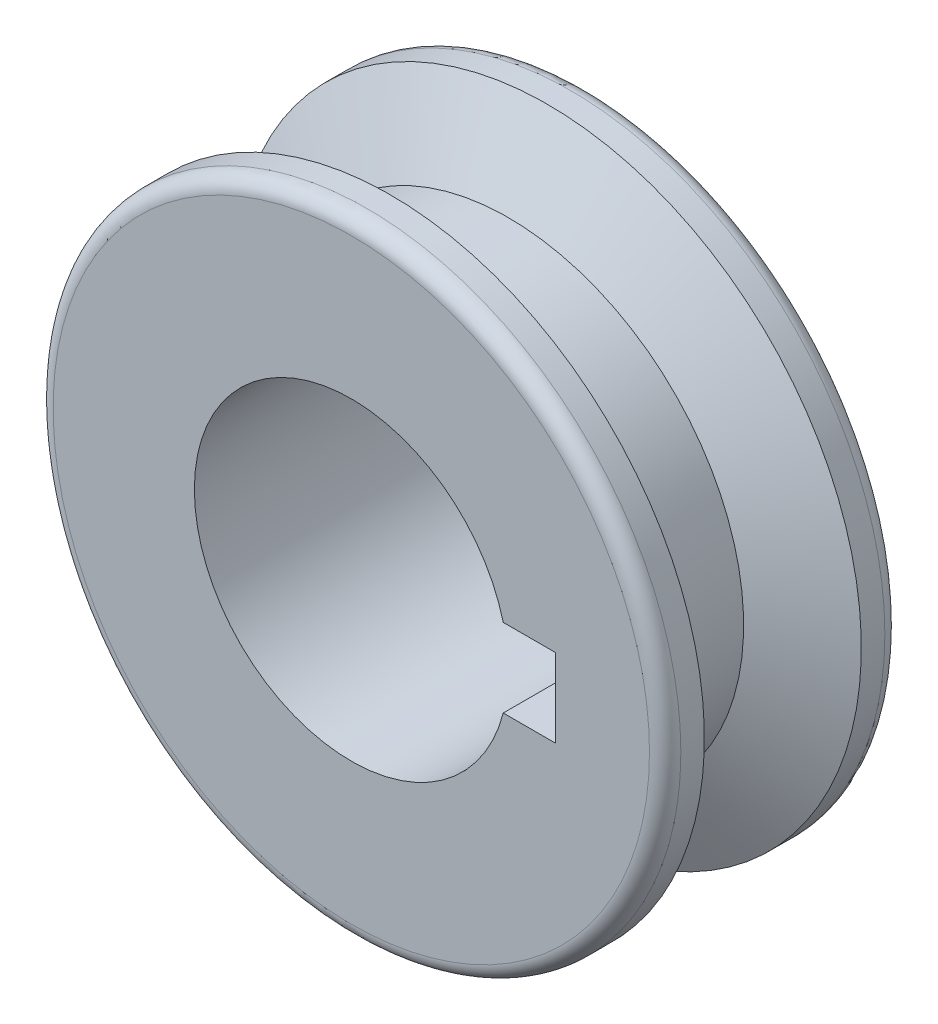
SolidWorks part; units mm, degrees
ref_plane "前视基准面" through (0, 0, 0) normal (0, 0, 1) x (1, 0, 0)
ref_plane "上视基准面" through (0, 0, 0) normal (0, 1, 0) x (1, 0, 0)
ref_plane "右视基准面" through (0, 0, 0) normal (1, 0, 0) x (0, 0, -1)
sketch "草图1" plane through (0, 0, 0) normal (0, 0, 1) x (1, 0, 0)
  circle A0 centre (0, 0) radius 10
  circle A1 centre (0, 0) radius 20
  dimension "D1" = 20
  dimension "D2" = 40
extrude "凸台-拉伸1" add sketch "草图1" along normal blind 15
sketch "草图2" plane through (0, 0, 0) normal (1, 0, 0) x (0, 0, -1)
  line L0 (0, 20) -> (-15, 20)
  line L1 (-15, 20) -> (-15, 15)
  line L2 (-15, 20) -> (-15, -20) construction
  line L3 (-15, 15) -> (0, 15)
  line L4 (0, -20) -> (0, 20) construction
  line L6 (-2.5, 20) -> (-5, 15)
  line L8 (-12.5, 20) -> (-10, 15)
  dimension "D1" = 5
  dimension "D2" = 2.5
ref_axis "基准轴1" through (0, 0, -0.75) along (0, 0, 1)
revolve "切除-旋转1" cut sketch "草图2" angle 360 about axis through (0, 0, -0.75) along (0, 0, 1)
ref_plane "基准面1" through (10, 0, 0) normal (1, 0, 0) x (0, 0, -1)
sketch "草图3" plane through (10, 0, 0) normal (1, 0, 0) x (0, 0, -1)
  line L0 (-15.7356, 0) -> (0, 0) construction
  line L1 (-15.7356, 2.5) -> (0, 2.5)
  line L2 (-15.7356, -2.5) -> (0, -2.5)
  arc A0 (-15.7356, 2.5) -> (-15.7356, -2.5) centre (-15.7356, 0) ccw
  arc A1 (0, -2.5) -> (0, 2.5) centre (0, 0) ccw
  point P3 (-7.8678, 0)
  dimension "D1" = 5
extrude "切除-拉伸1" cut sketch "草图3" against normal blind 10 and the other way blind 3
fillet "圆角1" radius 1 2 edges at (20, 0, 15) (20, 0, 0)
